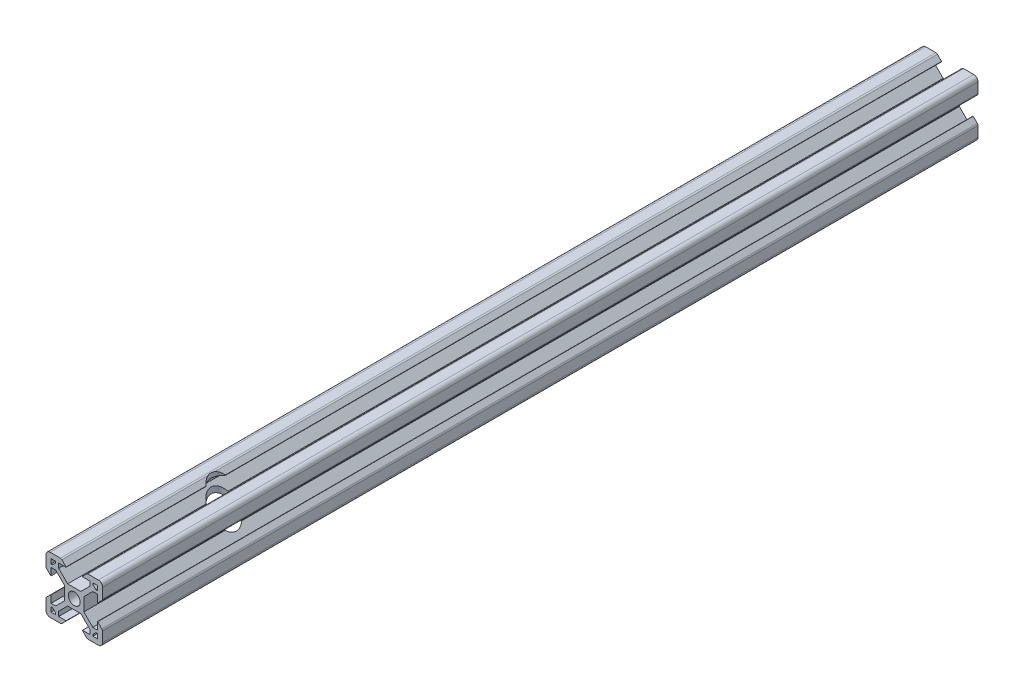
SolidWorks part; units mm, degrees
ref_plane "Front Plane" through (0, 0, 0) normal (0, 0, 1) x (1, 0, 0)
ref_plane "Top Plane" through (0, 0, 0) normal (0, 1, 0) x (1, 0, 0)
ref_plane "Right Plane" through (0, 0, 0) normal (1, 0, 0) x (0, 0, -1)
sketch "Sketch2" plane through (0, 0, 0) normal (0, 0, 1) x (1, 0, 0)
  line L0 (-8.2, 2.89) -> (-8.2, 5.5)
  line L1 (-2.1, 0) -> (-10, 0) construction
  line L2 (0, 2.1) -> (0, 10) construction
  line L3 (-4.9072, 10) -> (-8.5, 10)
  line L4 (-10, 4.9072) -> (-10, 8.5)
  line L5 (-2.1, 0) -> (-3.4, 0) construction
  line L6 (0, 2.1) -> (0, 3.4) construction
  line L7 (0, 3.4) -> (-2.3393, 3.4)
  line L8 (-3.4, 0) -> (-3.4, 2.3393)
  line L9 (-2.89, 8.2) -> (-5.5, 8.2)
  line L10 (-6.57, 8.2) -> (-6.57, 7.66)
  line L11 (-8.2, 6.57) -> (-7.66, 6.57)
  line L12 (-5.5, 8.2) -> (-5.5, 6.5607)
  line L13 (-6.5607, 5.5) -> (-8.2, 5.5)
  line L14 (-8.2, 8.2) -> (-1.4849, 1.4849) construction
  line L15 (-6.5607, 5.5) -> (-3.4, 2.3393)
  line L16 (-5.5, 6.5607) -> (-2.3393, 3.4)
  line L17 (-7.66, 6.57) -> (-6.57, 7.66)
  line L18 (-8.7303, 7.6697) -> (-0.5303, -0.5303) construction
  line L19 (-7.6697, 8.7303) -> (0.5303, 0.5303) construction
  line L20 (-8.2, 8.2) -> (0, 0) construction
  line L21 (-8.2, 6.57) -> (-8.2, 8.2)
  line L22 (-8.2, 0) -> (-8.2, 8.2) construction
  line L23 (-6.57, 8.2) -> (-8.2, 8.2)
  line L24 (0, 8.2) -> (-8.2, 8.2) construction
  line L25 (-10, 0) -> (-10, 10) construction
  line L26 (0, 10) -> (-10, 10) construction
  line L27 (-2.89, 8.31) -> (-2.89, 8.2)
  line L29 (-8.31, 2.89) -> (-8.2, 2.89)
  line L30 (-4.3486, 9.7686) -> (-2.89, 8.31)
  line L31 (-8.31, 2.89) -> (-9.7686, 4.3486)
  arc A0 (0, 2.1) -> (-2.1, 0) centre (0, 0) ccw
  arc A1 (-10, 8.5) -> (-8.5, 10) centre (-8.5, 8.5) cw
  arc A2 (-9.7686, 4.3486) -> (-10, 4.9072) centre (-9.21, 4.9072) cw
  arc A3 (-4.3486, 9.7686) -> (-4.9072, 10) centre (-4.9072, 9.21) ccw
  point P29 (-10, 10)
  point P39 (-10, 4.58)
  point P42 (-4.58, 10)
  dimension "D3" = 2.1
  dimension "D15" = 1.5
  dimension "D22" = 0.79
  dimension "D1" = 10
  dimension "D2" = 10
  dimension "D4" = 1.8
  dimension "D5" = 3.43
  dimension "D6" = 3.43
  dimension "D7" = 0.54
  dimension "D8" = 0.54
  dimension "D9" = 1.07
  dimension "D10" = 1.07
  dimension "D11" = 3.4
  dimension "D12" = 3.4
  dimension "D16" = 7.11
  dimension "D17" = 0.11
  dimension "D18" = 1.69
  dimension "D19" = 0.11
  dimension "D20" = 7.11
  dimension "D21" = 1.69
  dimension "D13" = 0.75
  dimension "D14" = 0.75
sketch "Sketch6" plane through (0, 0, 0) normal (0, 0, 1) x (1, 0, 0)
  line L0 (-3.4, 0) -> (-3.4, 2.3393) construction
  line L1 (-6.5607, 5.5) -> (-3.4, 2.3393) construction
  line L2 (-6.5607, 5.5) -> (-8.2, 5.5) construction
  line L3 (-8.2, 2.89) -> (-8.2, 5.5) construction
  line L4 (-8.31, 2.89) -> (-8.2, 2.89) construction
  line L5 (-7.66, 6.57) -> (-6.57, 7.66)
  line L6 (-6.57, 7.66) -> (-6.57, 8.2)
  line L7 (-6.57, 8.2) -> (-8.2, 8.2)
  line L8 (-8.2, 8.2) -> (-8.2, 6.57)
  line L9 (-8.2, 6.57) -> (-7.66, 6.57)
  line L10 (-7.66, 6.57) -> (-6.57, 7.66)
  line L11 (-6.57, 7.66) -> (-6.57, 8.2)
  line L12 (-6.57, 8.2) -> (-8.2, 8.2)
  line L13 (-8.2, 8.2) -> (-8.2, 6.57)
  line L14 (-8.2, 6.57) -> (-7.66, 6.57)
  line L15 (-8.31, 2.89) -> (-9.7686, 4.3486) construction
  line L16 (-10, 4.9072) -> (-10, 8.5) construction
  line L17 (-4.9072, 10) -> (-8.5, 10) construction
  line L18 (-4.3486, 9.7686) -> (-2.89, 8.31) construction
  line L19 (-2.89, 8.31) -> (-2.89, 8.2) construction
  line L20 (-2.89, 8.2) -> (-5.5, 8.2) construction
  line L21 (-5.5, 8.2) -> (-5.5, 6.5607) construction
  line L22 (-5.5, 6.5607) -> (-2.3393, 3.4) construction
  line L23 (0, 3.4) -> (-2.3393, 3.4) construction
  line L24 (-3.4, -2.3393) -> (-3.4, 2.3393)
  line L25 (-6.5607, 5.5) -> (-3.4, 2.3393)
  line L26 (-6.5607, 5.5) -> (-8.2, 5.5)
  line L27 (-8.2, 2.89) -> (-8.2, 5.5)
  line L28 (-8.31, 2.89) -> (-8.2, 2.89)
  line L29 (-8.31, 2.89) -> (-9.7686, 4.3486)
  line L30 (-10, 4.9072) -> (-10, 8.5)
  line L31 (-4.9072, 10) -> (-8.5, 10)
  line L32 (-4.3486, 9.7686) -> (-2.89, 8.31)
  line L33 (-2.89, 8.31) -> (-2.89, 8.2)
  line L34 (-2.89, 8.2) -> (-5.5, 8.2)
  line L35 (-5.5, 8.2) -> (-5.5, 6.5607)
  line L36 (-5.5, 6.5607) -> (-2.3393, 3.4)
  line L37 (2.3393, 3.4) -> (-2.3393, 3.4)
  line L38 (0, 2.1) -> (0, 10) construction
  line L39 (-2.1, 0) -> (-10, 0) construction
  line L40 (0, 2.1) -> (0, 10) construction
  line L41 (-2.1, 0) -> (-10, 0) construction
  line L42 (2.1, 0) -> (10, 0) construction
  line L43 (5.5, 6.5607) -> (2.3393, 3.4)
  line L44 (5.5, 8.2) -> (5.5, 6.5607)
  line L45 (2.89, 8.2) -> (5.5, 8.2)
  line L46 (2.89, 8.31) -> (2.89, 8.2)
  line L47 (4.3486, 9.7686) -> (2.89, 8.31)
  line L48 (4.9072, 10) -> (8.5, 10)
  line L49 (10, 4.9072) -> (10, 8.5)
  line L50 (8.31, 2.89) -> (9.7686, 4.3486)
  line L51 (8.31, 2.89) -> (8.2, 2.89)
  line L52 (8.2, 2.89) -> (8.2, 5.5)
  line L53 (6.5607, 5.5) -> (8.2, 5.5)
  line L54 (6.5607, 5.5) -> (3.4, 2.3393)
  line L55 (3.4, -2.3393) -> (3.4, 2.3393)
  line L56 (8.2, 6.57) -> (7.66, 6.57)
  line L57 (8.2, 8.2) -> (8.2, 6.57)
  line L58 (6.57, 8.2) -> (8.2, 8.2)
  line L59 (6.57, 7.66) -> (6.57, 8.2)
  line L60 (7.66, 6.57) -> (6.57, 7.66)
  line L61 (0, -2.1) -> (0, -10) construction
  line L62 (7.66, -6.57) -> (6.57, -7.66)
  line L63 (6.57, -7.66) -> (6.57, -8.2)
  line L64 (6.57, -8.2) -> (8.2, -8.2)
  line L65 (8.2, -8.2) -> (8.2, -6.57)
  line L66 (8.2, -6.57) -> (7.66, -6.57)
  line L67 (6.5607, -5.5) -> (3.4, -2.3393)
  line L68 (6.5607, -5.5) -> (8.2, -5.5)
  line L69 (8.2, -2.89) -> (8.2, -5.5)
  line L70 (8.31, -2.89) -> (8.2, -2.89)
  line L71 (8.31, -2.89) -> (9.7686, -4.3486)
  line L72 (10, -4.9072) -> (10, -8.5)
  line L73 (4.9072, -10) -> (8.5, -10)
  line L74 (4.3486, -9.7686) -> (2.89, -8.31)
  line L75 (2.89, -8.31) -> (2.89, -8.2)
  line L76 (2.89, -8.2) -> (5.5, -8.2)
  line L77 (5.5, -8.2) -> (5.5, -6.5607)
  line L78 (5.5, -6.5607) -> (2.3393, -3.4)
  line L79 (2.3393, -3.4) -> (-2.3393, -3.4)
  line L80 (-5.5, -6.5607) -> (-2.3393, -3.4)
  line L81 (-5.5, -8.2) -> (-5.5, -6.5607)
  line L82 (-2.89, -8.2) -> (-5.5, -8.2)
  line L83 (-2.89, -8.31) -> (-2.89, -8.2)
  line L84 (-4.3486, -9.7686) -> (-2.89, -8.31)
  line L85 (-4.9072, -10) -> (-8.5, -10)
  line L86 (-10, -4.9072) -> (-10, -8.5)
  line L87 (-8.31, -2.89) -> (-9.7686, -4.3486)
  line L88 (-8.31, -2.89) -> (-8.2, -2.89)
  line L89 (-8.2, -2.89) -> (-8.2, -5.5)
  line L90 (-6.5607, -5.5) -> (-8.2, -5.5)
  line L91 (-6.5607, -5.5) -> (-3.4, -2.3393)
  line L92 (-8.2, -6.57) -> (-7.66, -6.57)
  line L93 (-8.2, -8.2) -> (-8.2, -6.57)
  line L94 (-6.57, -8.2) -> (-8.2, -8.2)
  line L95 (-6.57, -7.66) -> (-6.57, -8.2)
  line L96 (-7.66, -6.57) -> (-6.57, -7.66)
  arc A0 (0, 2.1) -> (-2.1, 0) centre (0, 0) ccw construction
  arc A1 (-10, 4.9072) -> (-9.7686, 4.3486) centre (-9.21, 4.9072) ccw construction
  arc A2 (-8.5, 10) -> (-10, 8.5) centre (-8.5, 8.5) ccw construction
  arc A3 (-4.3486, 9.7686) -> (-4.9072, 10) centre (-4.9072, 9.21) ccw construction
  circle A4 centre (0, 0) radius 2.1
  arc A5 (-10, 4.9072) -> (-9.7686, 4.3486) centre (-9.21, 4.9072) ccw
  arc A6 (-8.5, 10) -> (-10, 8.5) centre (-8.5, 8.5) ccw
  arc A7 (-4.3486, 9.7686) -> (-4.9072, 10) centre (-4.9072, 9.21) ccw
  arc A8 (4.3486, 9.7686) -> (4.9072, 10) centre (4.9072, 9.21) cw
  arc A9 (8.5, 10) -> (10, 8.5) centre (8.5, 8.5) cw
  arc A10 (10, 4.9072) -> (9.7686, 4.3486) centre (9.21, 4.9072) cw
  arc A11 (10, -4.9072) -> (9.7686, -4.3486) centre (9.21, -4.9072) ccw
  arc A12 (8.5, -10) -> (10, -8.5) centre (8.5, -8.5) ccw
  arc A13 (4.3486, -9.7686) -> (4.9072, -10) centre (4.9072, -9.21) ccw
  arc A14 (-4.3486, -9.7686) -> (-4.9072, -10) centre (-4.9072, -9.21) cw
  arc A15 (-8.5, -10) -> (-10, -8.5) centre (-8.5, -8.5) cw
  arc A16 (-10, -4.9072) -> (-9.7686, -4.3486) centre (-9.21, -4.9072) cw
  point P85 (3.4, 0)
  dimension "D1" = 0
extrude "Boss-Extrude1" add sketch "Sketch6" against normal blind 310
ref_plane "Middle" through (0, 0, -155) normal (0, 0, 1) x (1, 0, 0)
sketch "Sketch7" plane through (0, 0, 0) normal (0, 1, 0) x (1, 0, 0)
  circle A0 centre (0, 52.93) radius 4.5
  dimension "D1" = 9
  dimension "D2" = 52.93
extrude "Cut-Extrude1" cut sketch "Sketch7" against normal through all and the other way through all
